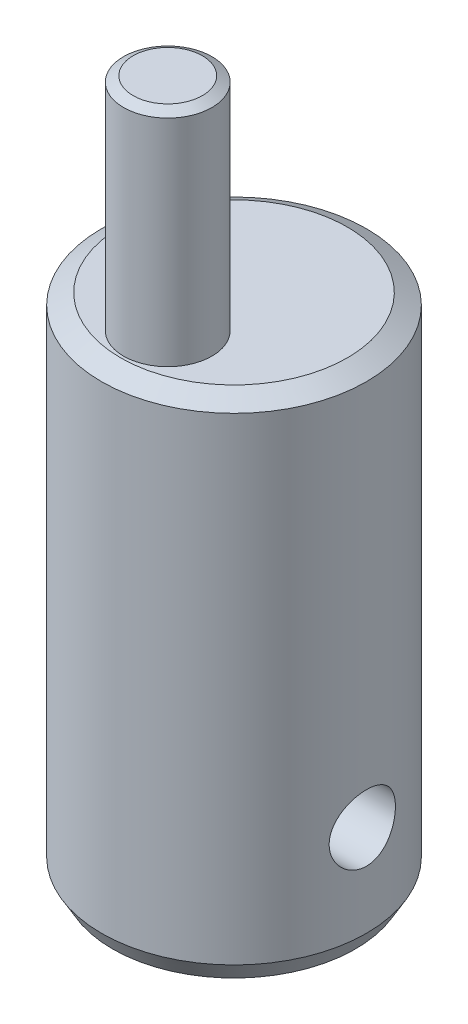
SolidWorks part; units mm, degrees
ref_plane "Front Plane" through (0, 0, 0) normal (0, 0, 1) x (1, 0, 0)
ref_plane "Top Plane" through (0, 0, 0) normal (0, 1, 0) x (1, 0, 0)
ref_plane "Right Plane" through (0, 0, 0) normal (1, 0, 0) x (0, 0, -1)
sketch "Sketch1" plane through (0, 0, 0) normal (0, 1, 0) x (1, 0, 0)
  circle A0 centre (0, 0) radius 6
  dimension "D1" = 12
extrude "Boss-Extrude1" add sketch "Sketch1" along normal blind 23
sketch "Sketch2" plane through (0, 23, 0) normal (0, 1, 0) x (1, 0, 0)
  circle A0 centre (0, -3) radius 2
  dimension "D2" = 4
  dimension "D1" = 3
extrude "Boss-Extrude2" add sketch "Sketch2" along normal blind 10
sketch "Sketch3" plane through (0, 0, 0) normal (1, 0, 0) x (0, 0, -1)
  line L0 (-6, 0) -> (6, 0) construction
  circle A0 centre (0, 5) radius 1.5
  dimension "D1" = 3
  dimension "D2" = 5
extrude "Cut-Extrude1" cut sketch "Sketch3" against normal through all both and the other way through all
chamfer "Chamfer1" distance 0.25 angle 60 1 edges at (0, 33, 5)
chamfer "Chamfer2" distance 0.5 angle 60 2 edges at (0, 0, 6) (0, 23, 6)
